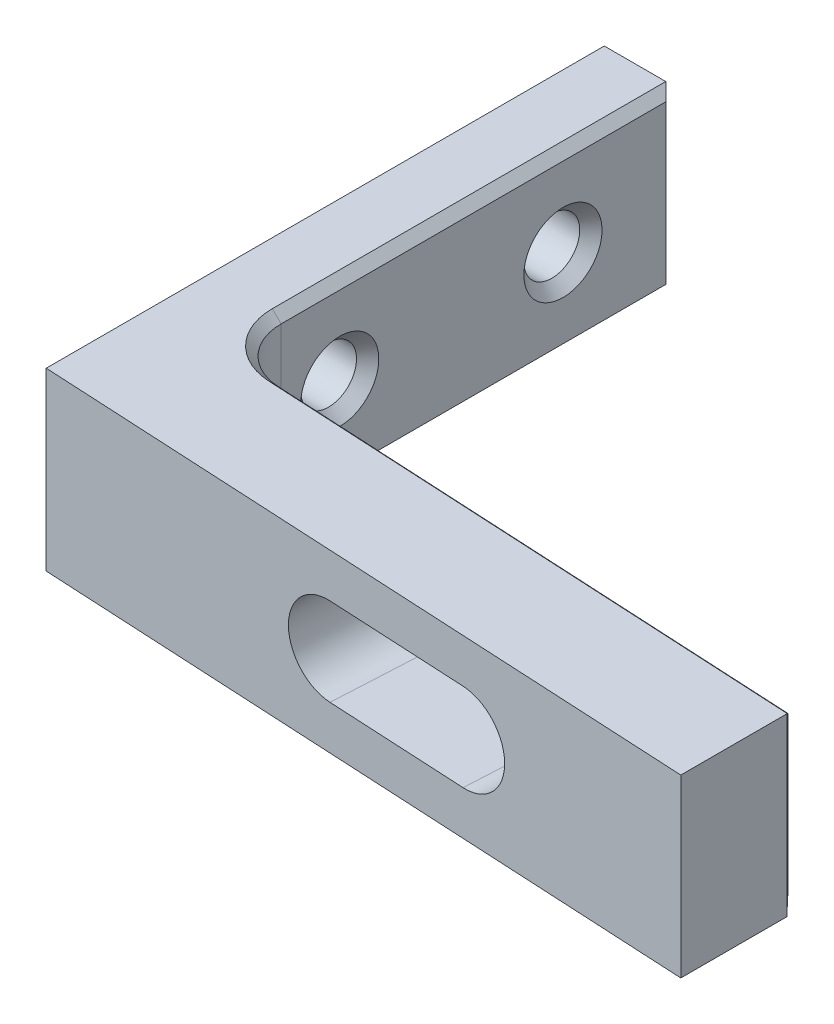
SolidWorks part; units mm, degrees
ref_plane "Front Plane" through (0, 0, 0) normal (0, 0, 1) x (1, 0, 0)
ref_plane "Top Plane" through (0, 0, 0) normal (0, 1, 0) x (1, 0, 0)
ref_plane "Right Plane" through (0, 0, 0) normal (1, 0, 0) x (0, 0, -1)
sketch "Sketch1" plane through (0, 0, 0) normal (0, 1, 0) x (1, 0, 0)
  line L1 (-19.05, -15.875) -> (19.05, -15.875)
  line L2 (-19.05, -15.875) -> (-19.05, 15.875)
  line L3 (-19.05, 15.875) -> (19.05, 15.875)
  line L4 (19.05, -15.875) -> (19.05, 15.875)
  line L5 (-19.05, -15.875) -> (19.05, 15.875) construction
  line L6 (-19.05, 15.875) -> (19.05, -15.875) construction
  point P0 (0, 0)
  dimension "D1" = 38.1
  dimension "D2" = 31.75
extrude "Boss-Extrude1" add sketch "Sketch1" along normal blind 10
sketch "Sketch2" plane through (0, 10, 0) normal (0, 1, 0) x (1, 0, 0)
  line L0 (-19.05, 15.875) -> (-19.05, -15.875) construction
  line L1 (19.05, 15.875) -> (-15.05, 15.875)
  line L2 (19.05, 15.875) -> (19.05, -9.525)
  line L3 (19.05, -9.525) -> (-15.05, -9.525)
  line L4 (-15.05, 15.875) -> (-15.05, -9.525)
  line L5 (-19.05, -15.875) -> (19.05, -15.875) construction
  dimension "D1" = 4
  dimension "D2" = 6.35
extrude "Cut-Extrude1" cut sketch "Sketch2" against normal up to next
hole_wizard "1/8 (0.125) Diameter Hole1" positions "Sketch4" profile "Sketch3" hole size "1/8" standard "Ansi Inch" end condition through all
sketch "Sketch4" plane through (-19.05, 0, 0) normal (-1, 0, 0) x (0, 0, 1)
  line L1 (-15.875, 5) -> (-9.525, 5) construction
  line L2 (-15.875, 10) -> (-15.875, 0) construction
  line L3 (3.175, 5) -> (-9.525, 5) construction
  line L4 (9.525, 0) -> (9.525, 10) construction
  point P0 (-9.525, 5)
  point P1 (3.175, 5)
  dimension "D1" = 6.35
  dimension "D2" = 12.7
sketch "Sketch3" plane through (-19.05, 5, -9.525) normal (0, 1, 0) x (0, 0, 1)
  line L0 (0, 0) -> (0, 4)
  line L1 (0, 4) -> (2.2225, 4)
  line L2 (1.5875, 3.365) -> (1.5875, 0.635)
  line L3 (1.5875, 0.635) -> (2.2225, 0)
  line L5 (2.2225, 0) -> (0, 0)
  line L6 (-1.5875, 0.635) -> (-2.2225, 0) construction
  line L7 (2.2225, 4) -> (1.5875, 3.365)
  line L8 (-2.2225, 4) -> (-1.5875, 3.365) construction
  line L11 (0, -6.35) -> (0, 107.95) construction
  dimension "Thru Hole Dia." = 3.175
  dimension "Thru Hole Depth" = 4
  dimension "Near C'Sink Dia." = 4.445
  dimension "Near C'Sink Angle" = 90
  dimension "Far C'Sink Dia." = 4.445
  dimension "Far C'Sink Angle" = 90
draft "Draft1" type of draft neutral plane draft angle 3 faces to draft 1 face at (0, 5, 15.875) neutral plane through (-19.05, 10, 15.875) neutral plane normal (-1, 0, 0) parameters "D1"=3
sketch "Sketch7" plane through (0, 10, 0) normal (0, 1, 0) x (1, 0, 0)
  line L0 (-15.05, -9.525) -> (19.05, -9.525) construction
  line L1 (-15.05, -9.525) -> (19.05, -9.525)
  line L2 (19.05, -17.8717) -> (19.05, -9.525) construction
  line L3 (19.05, -11.3121) -> (19.05, -9.525)
  line L4 (-15.05, -9.525) -> (19.05, -11.3121)
  line L5 (-19.05, -15.875) -> (19.05, -17.8717) construction
extrude "Cut-Extrude2" cut sketch "Sketch7" against normal through all
sketch "Sketch8" plane through (-0.539, 0, 10.2855) normal (0.0523, 0, -0.9986) x (-0.9986, 0, -0.0523)
  line L0 (-6.8691, 5) -> (1.1309, 5) construction
  line L1 (-6.8691, 7.5) -> (1.1309, 7.5)
  line L2 (-6.8691, 2.5) -> (1.1309, 2.5)
  line L3 (-19.6159, 5) -> (-6.8691, 5) construction
  line L4 (-19.6159, 0) -> (-19.6159, 10) construction
  line L8 (14.5309, 0) -> (14.5309, 10) construction
  arc A0 (-6.8691, 7.5) -> (-6.8691, 2.5) centre (-6.8691, 5) ccw
  arc A1 (1.1309, 2.5) -> (1.1309, 7.5) centre (1.1309, 5) ccw
  point P2 (-2.8691, 5)
  dimension "D2" = 8
  dimension "D1" = 5
  dimension "D3" = 21.4
extrude "Cut-Extrude3" cut sketch "Sketch8" against normal through all
fillet "Fillet2" radius 3.175 1 edges at (-15.05, 5, 9.525)
chamfer "Chamfer1" distance 0.5 angle 45 4 edges at (2.3262, 7.5, 10.4356) (8.8172, 5, 10.7758) (-4.1649, 5, 10.0955) (2.3262, 2.5, 10.4356)
chamfer "Chamfer2" distance 0.5 angle 45 8 edges at (-15.05, 0, -4.6815) (-14.1781, 0, 8.6976) (3.5044, 0, 10.4974) (-15.05, 10, -4.6815) (-14.1781, 10, 8.6976) (3.5044, 10, 10.4974) (19.05, 5, 11.3121) (-15.05, 5, -15.875)
